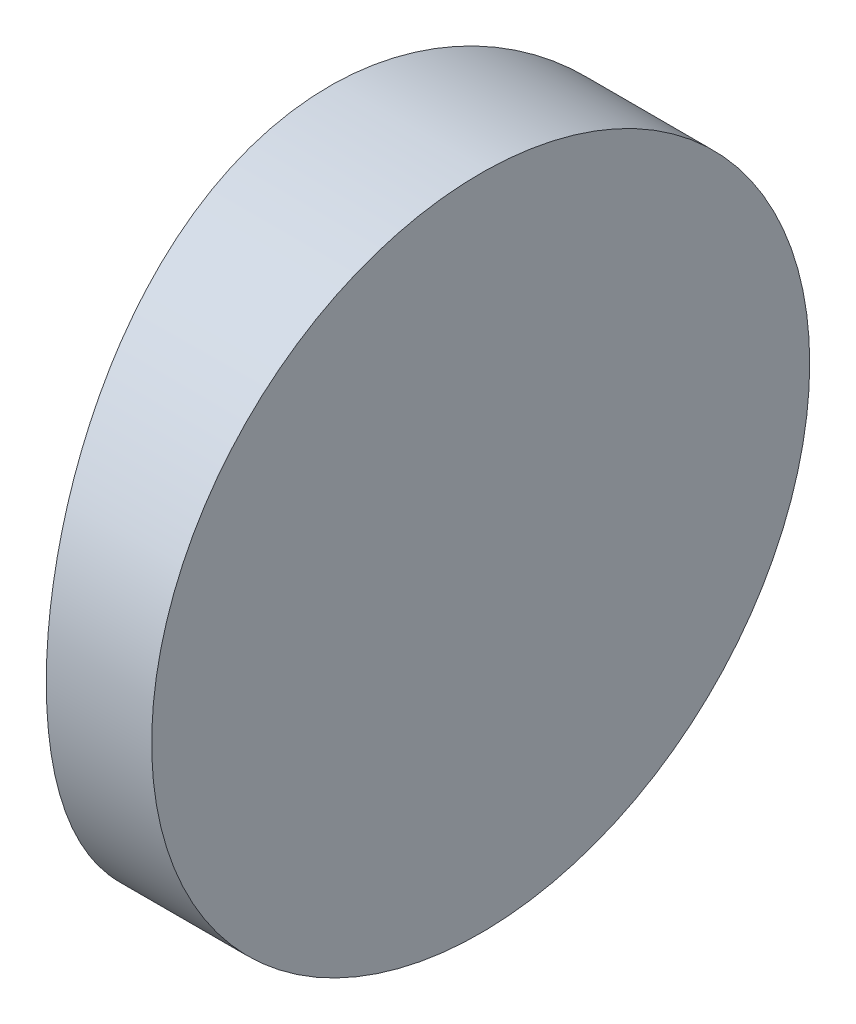
SolidWorks part; units mm, degrees
ref_plane "前视基准面" through (0, 0, 0) normal (0, 0, 1) x (1, 0, 0)
ref_plane "上视基准面" through (0, 0, 0) normal (0, 1, 0) x (1, 0, 0)
ref_plane "右视基准面" through (0, 0, 0) normal (1, 0, 0) x (0, 0, -1)
sketch "草图1" plane through (0, 0, 0) normal (0, 1, 0) x (1, 0, 0)
  line L0 (10.7432, 0) -> (-20.3908, 0) construction
  line L1 (-17.7066, 6.25) -> (-15.7048, 6.25)
  line L2 (-17.7066, -6.25) -> (-15.7048, -6.25)
  line L3 (-15.7048, 6.25) -> (-15.7048, -6.25)
  arc A0 (-17.7066, 6.25) -> (-17.7066, -6.25) centre (4.3552, 0) ccw
  point P2 (-20.3908, 0)
  point P19 (-18.5748, 0)
  point P20 (-15.7048, 0)
  dimension "D2" = 6.25
  dimension "D3" = 22.93
  dimension "D4" = 2.87
  dimension "D1" = 6.25
extrude "凸台-拉伸1" add sketch "草图1" along normal blind 12.5 contours A0 L2 L3 L1
sketch "草图2" plane through (-15.7048, 0, 0) normal (1, 0, 0) x (0, 0, -1)
  line L0 (6.25, 0) -> (-6.25, 0) construction
  line L7 (-6.25, 0) -> (6.25, 0)
  line L8 (6.25, 0) -> (6.25, 12.5)
  line L9 (6.25, 12.5) -> (-6.25, 12.5)
  line L10 (-6.25, 12.5) -> (-6.25, 0)
  line L11 (-6.25, 0) -> (6.25, 0)
  line L12 (6.25, 0) -> (6.25, 12.5)
  line L13 (6.25, 12.5) -> (-6.25, 12.5)
  line L14 (-6.25, 12.5) -> (-6.25, 0)
  circle A0 centre (0, 6.25) radius 6.25
  line M1 (-6.25, 0) -> (6.25, 0)
  line M2 (6.25, 0) -> (6.25, 12.5)
  line M3 (6.25, 12.5) -> (-6.25, 12.5)
  line M4 (-6.25, 12.5) -> (-6.25, 0)
  dimension "D1" = 12.5
  dimension "D2" = 6.25
  dimension "D3" = 0
extrude "切除-拉伸8" cut sketch "草图2" against normal blind 12.7 contours A0 L13 M4 | A0 L12 M3 | A0 L11 M2 | A0 L14 M1
